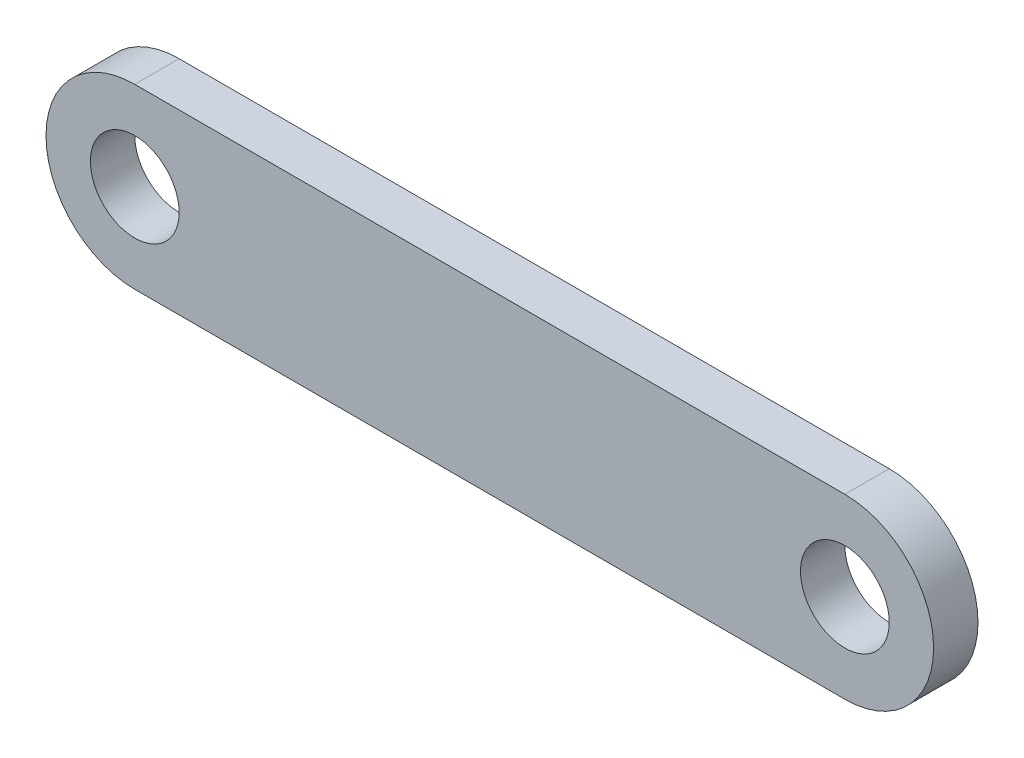
SolidWorks part; units mm, degrees
ref_plane "Front Plane" through (0, 0, 0) normal (0, 0, 1) x (1, 0, 0)
ref_plane "Top Plane" through (0, 0, 0) normal (0, 1, 0) x (1, 0, 0)
ref_plane "Right Plane" through (0, 0, 0) normal (1, 0, 0) x (0, 0, -1)
sketch "Sketch1" plane through (0, 0, 0) normal (0, 0, 1) x (1, 0, 0)
  line L0 (-16, 0) -> (16, 0) construction
  line L1 (-16, 4) -> (16, 4)
  line L2 (-16, -4) -> (16, -4)
  arc A0 (-16, 4) -> (-16, -4) centre (-16, 0) ccw
  arc A1 (16, -4) -> (16, 4) centre (16, 0) ccw
  circle A2 centre (-16, 0) radius 2
  circle A3 centre (16, 0) radius 2
  point P3 (0, 0)
  dimension "D3" = 4
  dimension "D4" = 4
  dimension "D1" = 32
  dimension "D2" = 8
extrude "Boss-Extrude2" add sketch "Sketch1" along normal mid plane 2
